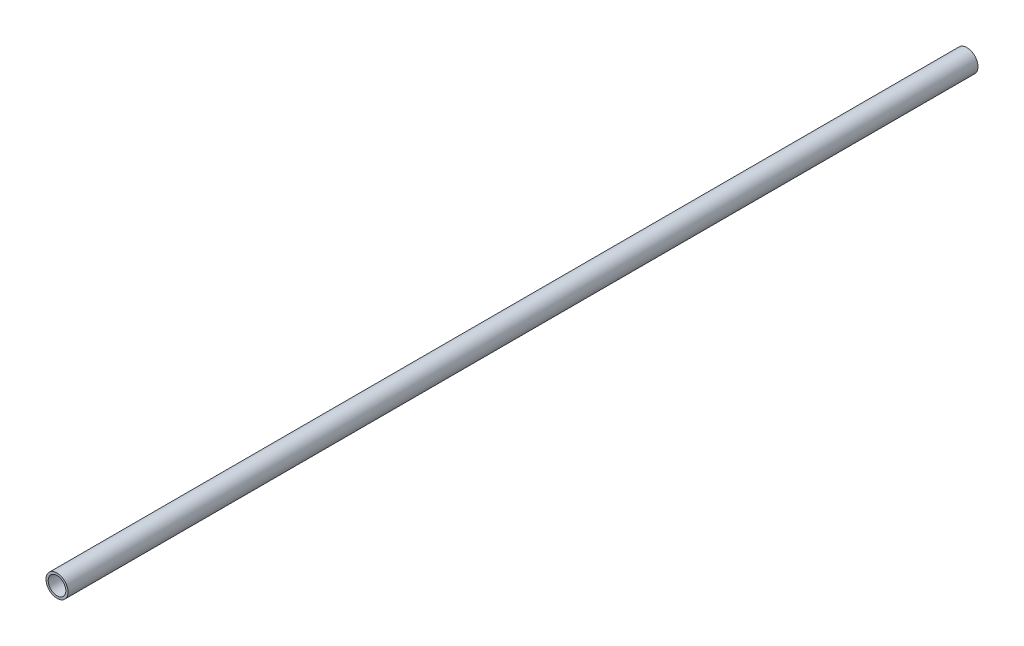
SolidWorks part; units mm, degrees
ref_plane "Front Plane" through (0, 0, 0) normal (0, 0, 1) x (1, 0, 0)
ref_plane "Top Plane" through (0, 0, 0) normal (0, 1, 0) x (1, 0, 0)
ref_plane "Right Plane" through (0, 0, 0) normal (1, 0, 0) x (0, 0, -1)
sketch "Sketch1" plane through (0, 0, 0) normal (0, 0, 1) x (1, 0, 0)
  circle A0 centre (0, 0) radius 2
  circle A1 centre (0, 0) radius 2.5
  dimension "D1" = 5
  dimension "D2" = 4
extrude "Boss-Extrude1" add sketch "Sketch1" along normal blind 206.375
